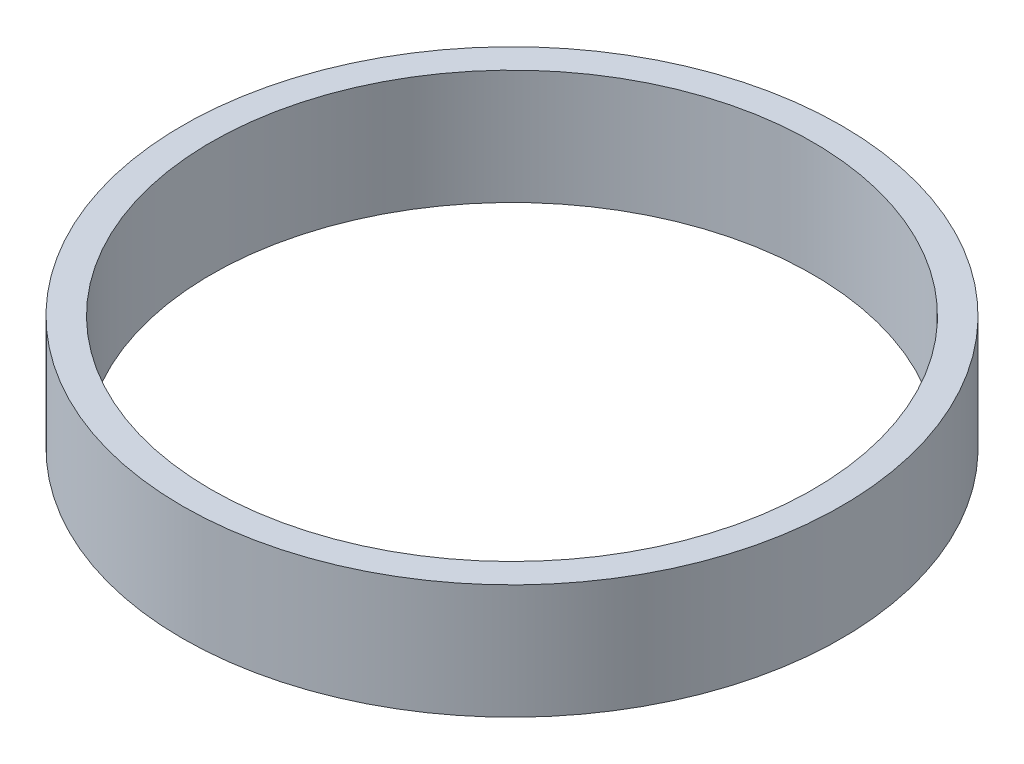
SolidWorks part; units mm, degrees
ref_plane "Front Plane" through (0, 0, 0) normal (0, 0, 1) x (1, 0, 0)
ref_plane "Top Plane" through (0, 0, 0) normal (0, 1, 0) x (1, 0, 0)
ref_plane "Right Plane" through (0, 0, 0) normal (1, 0, 0) x (0, 0, -1)
sketch "Sketch1" plane through (0, 0, 0) normal (0, 1, 0) x (1, 0, 0)
  circle A0 centre (0, 0) radius 10.5
  circle A1 centre (0, 0) radius 11.5
  point P4 (0, 0)
  dimension "D1" = 21
  dimension "D2" = 1
extrude "Boss-Extrude1" add sketch "Sketch1" along normal blind 4
